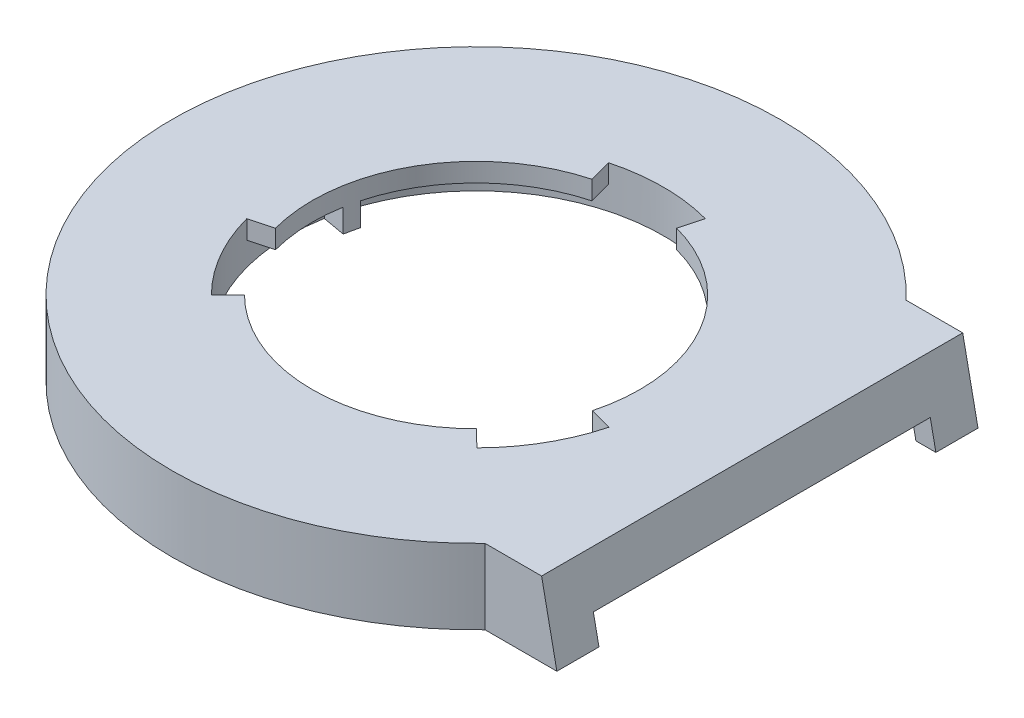
SolidWorks part; units mm, degrees
material "ABS"
ref_plane "Front Plane" through (0, 0, 0) normal (0, 0, 1) x (1, 0, 0)
ref_plane "Top Plane" through (0, 0, 0) normal (0, 1, 0) x (1, 0, 0)
ref_plane "Right Plane" through (0, 0, 0) normal (1, 0, 0) x (0, 0, -1)
sketch "Sketch1" plane through (0, 0, 0) normal (0, 1, 0) x (1, 0, 0)
  line L0 (25, 44.9998) -> (69, 44.9998)
  line L1 (25, 44.9998) -> (25, -45.0002)
  line L2 (25, -45.0002) -> (69, -45.0002)
  line L3 (69, 44.9998) -> (69, -45.0002)
  circle A0 centre (0, 0) radius 65
  dimension "D1" = 130
  dimension "D2" = 90
  dimension "D3" = 51.478
  dimension "D4" = 25
  dimension "D5" = 51.4783
  dimension "D6" = 69
extrude "Boss-Extrude1" add sketch "Sketch1" along normal blind 16 contours L0 A0 L2 L1 | A0 L2 L3 L0 | L2 A0 L0 L1
sketch "Sketch3" plane through (0, 0, 0) normal (0, -1, 0) x (1, 0, 0)
  line L0 (46.904, 45.0002) -> (69, 45.0002) construction
  line L1 (64, 40.2002) -> (13.6488, 40.2002)
  line L2 (64, 40.2002) -> (64, -40.1998)
  line L3 (64, -40.1998) -> (13.6488, -40.1998)
  line L4 (13.6488, 40.2002) -> (13.6488, -40.1998)
  line L5 (46.9043, -44.9998) -> (69, -44.9998) construction
  line L6 (69, -44.9998) -> (69, 45.0002) construction
  circle A1 centre (0, 0) radius 60
  dimension "D1" = 120
  dimension "D2" = 4.8
  dimension "D3" = 4.8
  dimension "D4" = 5
extrude "Cut-Extrude1" cut sketch "Sketch3" against normal blind 12
sketch "Sketch4" plane through (69, 0, 0) normal (1, 0, 0) x (0, 0, -1)
  line L0 (44.9998, 0) -> (-45.0002, 0) construction
  line L1 (-36.0002, 5) -> (35.9998, 5)
  line L2 (-36.0002, 5) -> (-36.0002, 0)
  line L3 (-36.0002, 0) -> (35.9998, 0)
  line L4 (35.9998, 5) -> (35.9998, 0)
  line L5 (-45.0002, 16) -> (-45.0002, 0) construction
  dimension "D1" = 72
  dimension "D2" = 5
  dimension "D3" = 9
extrude "Cut-Extrude2" cut sketch "Sketch4" against normal blind 16
sketch "Sketch5" plane through (0, 16, 0) normal (0, 1, 0) x (1, 0, 0)
  circle A0 centre (0, 0) radius 35
  dimension "D1" = 70
extrude "Cut-Extrude3" cut sketch "Sketch5" against normal blind 16
sketch "Sketch6" plane through (0, 16, 0) normal (0, 1, 0) x (1, 0, 0)
  line L7 (-24.7487, -24.7487) -> (-28.2843, -28.2843)
  line L8 (-33.8074, -9.0587) -> (-38.637, -10.3528)
  line L9 (24.8135, -24.6838) -> (28.3583, -28.2101)
  line L10 (33.831, -8.9701) -> (38.664, -10.2515)
  line L11 (-9.0587, 33.8074) -> (-10.3528, 38.637)
  line L12 (9.0587, 33.8074) -> (10.3528, 38.637)
  line L13 (-34.641, -20) -> (-30.3109, -17.5)
  line L14 (34.6933, -19.9092) -> (30.3566, -17.4205)
  arc A0 (-38.637, -10.3528) -> (-28.2843, -28.2843) centre (0, 0) ccw
  arc A1 (-33.8074, -9.0587) -> (-24.7487, -24.7487) centre (0, 0) ccw
  arc A3 (9.0587, 33.8074) -> (-9.0587, 33.8074) centre (0, 0) ccw
  arc A4 (10.3528, 38.637) -> (-10.3528, 38.637) centre (0, 0) ccw
  arc A5 (24.8135, -24.6838) -> (33.831, -8.9701) centre (0, 0) ccw
  arc A6 (28.3583, -28.2101) -> (38.664, -10.2515) centre (0, 0) ccw
  circle M1 centre (0, 0) radius 35
  dimension "D1" = 80
  dimension "D2" = 5
  dimension "D3" = 5
  dimension "D4" = 15
  dimension "D5" = 165
  dimension "D6" = 15
  dimension "D7" = 165
extrude "Cut-Extrude4" cut sketch "Sketch6" against normal blind 10 contours L13 A0 L7 M1 | L8 A0 L13 M1 | L12 A4 L11 M1 | L14 A6 L10 M1 | L9 A6 L14 M1
sketch "Sketch7" plane through (0, 12, 0) normal (0, -1, 0) x (1, 0, 0)
  line L11 (10.3528, 38.637) -> (9.0587, 33.8074)
  line L12 (13.6808, 37.5877) -> (11.9707, 32.8892)
  line L14 (28.2843, -28.2843) -> (24.7487, -24.7487)
  line L15 (25.7115, -30.6418) -> (22.4976, -26.8116)
  line L17 (-38.637, -10.3528) -> (-33.8074, -9.0587)
  line L18 (-39.3923, -6.9459) -> (-34.4683, -6.0777)
  circle A0 centre (0, 0) radius 42
  arc A1 (28.2843, -28.2843) -> (13.6808, 37.5877) centre (0, 0) ccw
  circle A3 centre (0, 0) radius 35
  arc A5 (-38.637, -10.3528) -> (25.7115, -30.6418) centre (0, 0) ccw
  arc A6 (10.3528, 38.637) -> (-39.3923, -6.9459) centre (0, 0) ccw
  arc M5 (-38.637, 10.3528) -> (-28.2843, 28.2843) centre (0, 0) cw
  arc M7 (-24.7487, 24.7487) -> (24.8135, 24.6838) centre (0, 0) cw
  arc M9 (28.3583, 28.2101) -> (38.664, 10.2515) centre (0, 0) cw
  arc M11 (33.831, 8.9701) -> (9.0587, -33.8074) centre (0, 0) cw
  arc M13 (10.3528, -38.637) -> (-10.3528, -38.637) centre (0, 0) cw
  arc M15 (-9.0587, -33.8074) -> (-33.8074, 9.0587) centre (0, 0) cw
  dimension "D1" = 84
  dimension "D2" = 80
  dimension "D3" = 70
  dimension "D10" = 5
  dimension "D11" = 5
  dimension "D12" = 5
extrude "Boss-Extrude2" add sketch "Sketch7" along normal blind 5 contours A0 A6 L11 L12 A1 L14 L15 A5 L17 L18 M7 M9 M11 M13 M15 M5
sketch "Sketch8" plane through (0, 12, 0) normal (0, -1, 0) x (1, 0, 0)
  circle A1 centre (44.5415, 40.2002) radius 1.5
  circle A4 centre (-25.2123, 54.4458) radius 3.5
  circle A5 centre (-25, -54.5436) radius 3.5
  circle A6 centre (44.5415, 40.2002) radius 3.5
  circle A7 centre (44.5418, -40.1998) radius 3.5
  circle A8 centre (-25.2123, 54.4458) radius 1.5
  circle A9 centre (-25, -54.5436) radius 1.5
  circle A10 centre (44.5418, -40.1998) radius 1.5
  circle A11 centre (0, 0) radius 60
  dimension "D1" = 3
  dimension "D2" = 60
  dimension "D3" = 7
  dimension "D4" = 7
  dimension "D5" = 7
  dimension "D6" = 3
  dimension "D7" = 3
  dimension "D8" = 3
  dimension "D12" = 120
  dimension "D9" = 60
  dimension "D10" = 7
  dimension "D11" = 108.9895
  dimension "D13" = 25
extrude "Boss-Extrude3" add sketch "Sketch8" along normal blind 12
sketch "Sketch13" plane through (0, 12, 0) normal (0, -1, 0) x (1, 0, 0)
  circle A0 centre (44.5415, 40.2002) radius 1.5
  circle A1 centre (-25.2123, 54.4458) radius 1.5
  circle A3 centre (-25, -54.5436) radius 1.5
  circle A5 centre (44.5418, -40.1998) radius 1.5
  arc A6 (-26.3557, -53.9016) -> (-23.6287, -55.1515) centre (0, 0) ccw construction
  arc A7 (-23.8434, 55.059) -> (-26.5654, 53.7985) centre (0, 0) ccw construction
extrude "Cut-Extrude5" cut sketch "Sketch13" along normal blind 12
sketch "Sketch14" plane through (0, 0, -44.9998) normal (0, 0, -1) x (-1, 0, 0)
  line L0 (-46.9043, 16) -> (-69, 16) construction
  line L1 (-69, 16) -> (-59, 16)
  line L2 (-69, 16) -> (-69, -33)
  line L5 (-59, 16) -> (-69, -33)
  line L6 (-69, 16) -> (-69, 0) construction
  point P1 (-69, 16)
  dimension "D1" = 10
  dimension "D2" = 49
sketch "Sketch15" plane through (0, 0, 45.0002) normal (0, 0, 1) x (1, 0, 0)
  line L0 (69, 16) -> (69, 0) construction
  line L1 (69, 16) -> (54.7644, 16)
  line L2 (69, 16) -> (69, 0)
  line L3 (69, 0) -> (54.7644, 0)
  line L4 (54.7644, 16) -> (54.7644, 0)
  line L5 (46.904, 0) -> (69, 0) construction
  point P6 (49.9058, 0)
  dimension "D1" = 14.2356
extrude "Boss-Extrude4" add sketch "Sketch15" against normal blind 90
extrude "Cut-Extrude6" cut sketch "Sketch14" against normal blind 90
sketch "Sketch17" plane through (0, 0, 45.0002) normal (0, 0, 1) x (1, 0, 0)
  line L8 (58, 0) -> (54.7347, 0)
  line L11 (54.7347, 0) -> (54.7347, 12)
  line L12 (55.551, 12) -> (58, 0)
  line L13 (54.7347, 12) -> (55.551, 12)
  dimension "D1" = 4.2653
  dimension "D2" = 12
extrude "Cut-Extrude11" cut sketch "Sketch17" against normal blind 80.4 from offset 4.8 offset against normal yes
sketch "Sketch19" plane through (59.7757, 12.1991, 0) normal (0.9798, 0.2, 0) x (0, 0, -1)
  line L0 (44.9998, -12.4506) -> (-45.0002, -12.4506) construction
  line L1 (-36.0002, -12.4506) -> (35.9998, -12.4506)
  line L2 (-36.0002, -12.4506) -> (-36.0002, -6.4506)
  line L3 (-36.0002, -6.4506) -> (35.9998, -6.4506)
  line L4 (35.9998, -12.4506) -> (35.9998, -6.4506)
  line L5 (-45.0002, -12.4506) -> (-45.0002, 3.8792) construction
  dimension "D1" = 9
  dimension "D2" = 72
  dimension "D3" = 6
extrude "Cut-Extrude14" cut sketch "Sketch19" against normal blind 8.4
